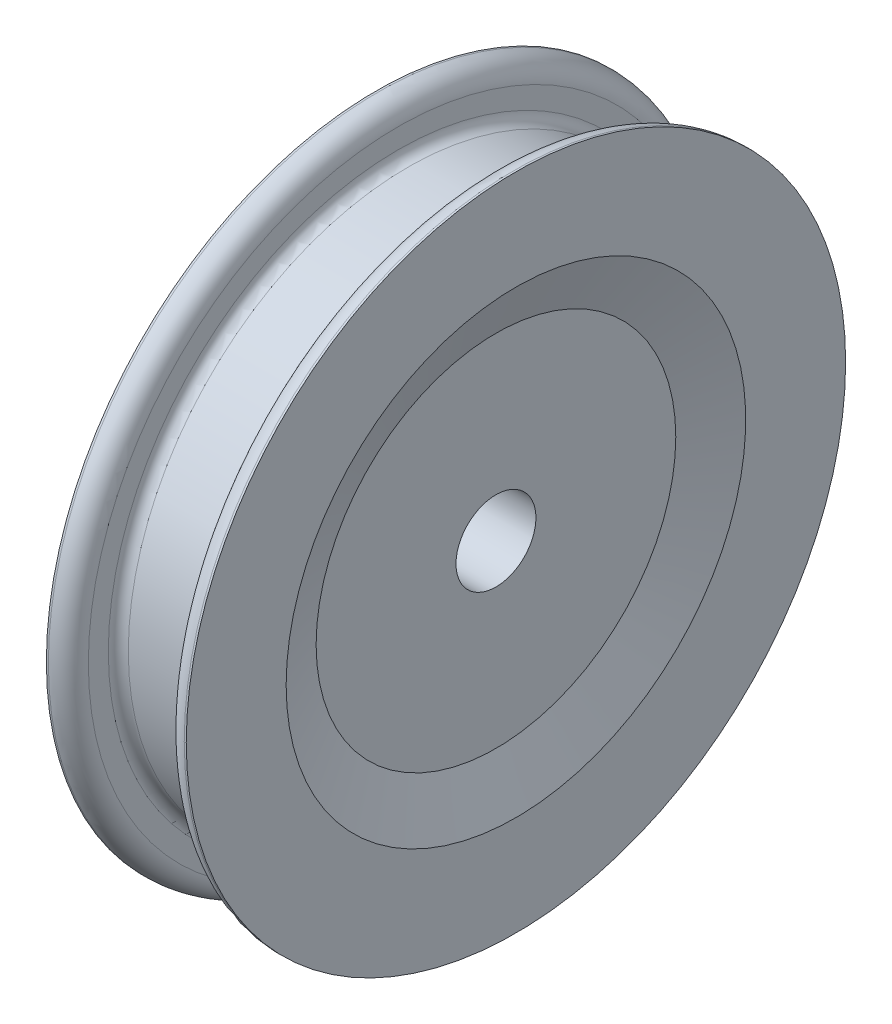
SolidWorks part; units mm, degrees
ref_plane "Front" through (0, 0, 0) normal (0, 0, 1) x (1, 0, 0)
ref_plane "Top" through (0, 0, 0) normal (0, 1, 0) x (1, 0, 0)
ref_plane "Right" through (0, 0, 0) normal (1, 0, 0) x (0, 0, -1)
sketch "Sketch1" plane through (0, 0, 0) normal (0, 0, 1) x (1, 0, 0)
  line L2 (1.75, 8.25) -> (1.2, 8.25)
  line L3 (1.2, 8.25) -> (1.2, 7.25)
  line L4 (0.95, 7) -> (-0.95, 7)
  line L5 (0, 7) -> (0, 1) construction
  line L6 (0, 0) -> (4.984, 0) construction
  line L7 (-1.2, 8.25) -> (-1.2, 7.25)
  line L8 (-1.75, 8.25) -> (-1.2, 8.25)
  line L10 (1.75, 8.25) -> (1.75, 5.75)
  line L11 (1.75, 5.75) -> (1.25, 4.5)
  line L12 (1.25, 4.5) -> (1.25, 1)
  line L15 (-1.75, 8.25) -> (-1.75, 1)
  line L16 (1.25, 1) -> (-1.75, 1)
  arc A0 (1.2, 7.25) -> (0.95, 7) centre (0.95, 7.25) cw
  arc A1 (-1.2, 7.25) -> (-0.95, 7) centre (-0.95, 7.25) ccw
  point P9 (0, 7)
  point P16 (1.2, 7)
  point P19 (-1.2, 7)
  dimension "D6" = 0.25
  dimension "D1" = 3
  dimension "D2" = 14
  dimension "D3" = 16.5
  dimension "D5" = 2.4
  dimension "D7" = 3.5
  dimension "D8" = 3.5
  dimension "D9" = 2.5
revolve "Revolve1" add sketch "Sketch1" angle 360 about L6
ref_point "Point1"
fillet "Fillet1" radius 0.5 2 edges at (-1.2, 0, 8.25) (1.2, 0, 8.25)
